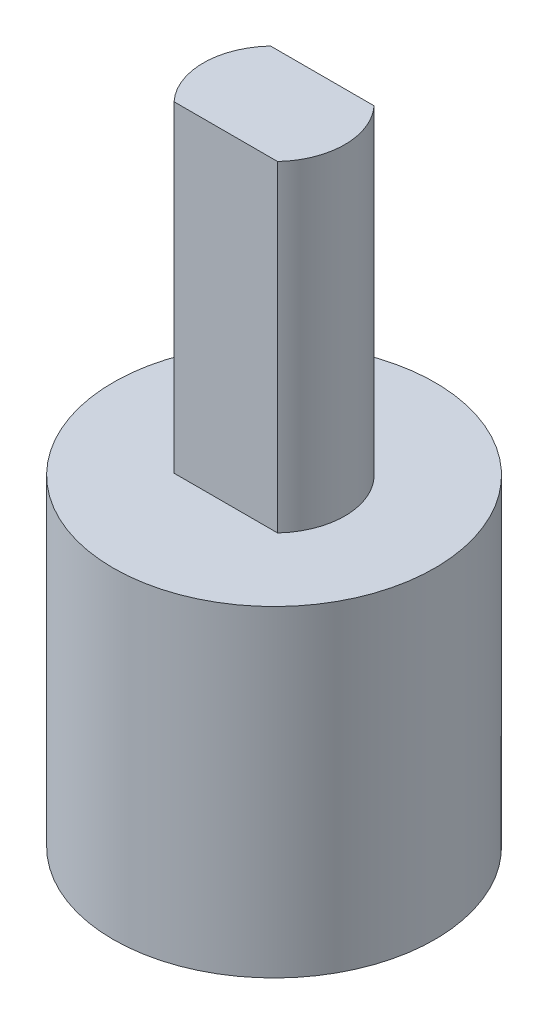
SolidWorks part; units mm, degrees
ref_plane "Front Plane" through (0, 0, 0) normal (0, 0, 1) x (1, 0, 0)
ref_plane "Top Plane" through (0, 0, 0) normal (0, 1, 0) x (1, 0, 0)
ref_plane "Right Plane" through (0, 0, 0) normal (1, 0, 0) x (0, 0, -1)
sketch "Sketch1" plane through (0, 0, 0) normal (0, 1, 0) x (1, 0, 0)
  line L0 (-2, 1.5) -> (2, 1.5)
  arc A0 (-2, 1.5) -> (2, 1.5) centre (0, 0) ccw
  circle A1 centre (0, 0) radius 5
  dimension "D1" = 5
  dimension "D3" = 10
  dimension "D2" = 4
extrude "Boss-Extrude1" add sketch "Sketch1" along normal blind 8
sketch "Sketch2" plane through (0, 8, 0) normal (0, 1, 0) x (1, 0, 0)
  circle A4 centre (0, 0) radius 5
  circle A5 centre (0, 0) radius 5
  dimension "D1" = 0
extrude "Boss-Extrude2" add sketch "Sketch2" along normal blind 2
sketch "Sketch3" plane through (0, 10, 0) normal (0, 1, 0) x (1, 0, 0)
  line L0 (-1.6093, 1.5) -> (1.6093, 1.5)
  line L1 (-1.6093, -1.5) -> (1.6093, -1.5)
  arc A0 (-1.6093, 1.5) -> (-1.6093, -1.5) centre (0, 0) ccw
  arc A3 (1.6093, -1.5) -> (1.6093, 1.5) centre (0, 0) ccw
  point P0 (0, 0)
  dimension "D2" = 4.4
  dimension "D3" = 1.5
  dimension "D4" = 1.5
extrude "Boss-Extrude3" add sketch "Sketch3" along normal blind 10
